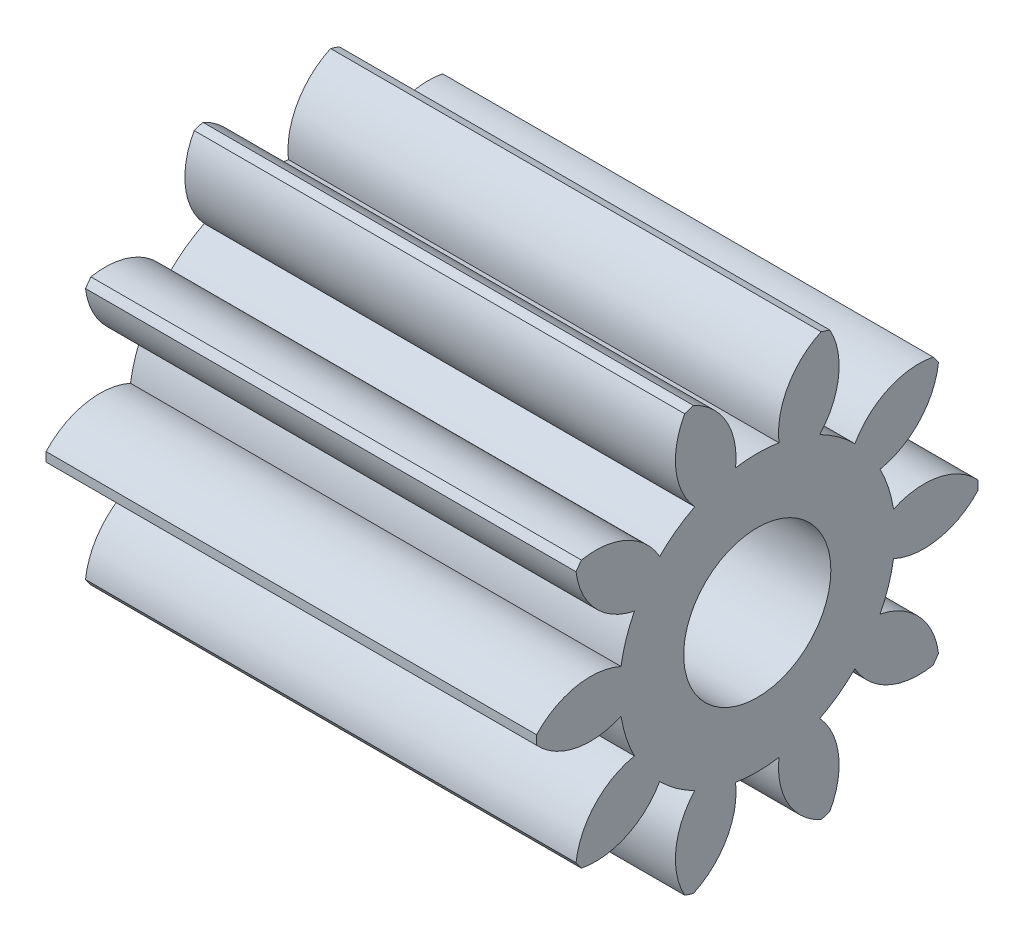
SolidWorks part; units mm, degrees
ref_plane "Plane1" through (0, 0, 0) normal (0, 0, 1) x (1, 0, 0)
ref_plane "Plane2" through (0, 0, 0) normal (0, 1, 0) x (1, 0, 0)
ref_plane "Plane3" through (0, 0, 0) normal (1, 0, 0) x (0, 0, -1)
sketch "HoldingSke" plane through (0, 0, 0) normal (0, 1, 0) x (1, 0, 0)
  line L0 (0, 0) -> (0.6565, -0.1158)
  line L1 (-15, 0) -> (100, 0) construction
  line L2 (0, 0) -> (-2.1039, 2.3779)
  line L3 (0, 0) -> (-11.863, 4.5341)
  line L4 (0, 0) -> (8.5048, 1.4996)
  line L5 (0, 0) -> (-46.8476, -17.4728)
  line L6 (0, 0) -> (-16.5793, -11.1861)
  line L7 (-2.1039, 2.3779) -> (8.6586, 51.2059)
  line L8 (-76.2, 54.61) -> (-75.3, 54.61)
  line L9 (-71.009, 38.7566) -> (-53.1078, 45.2721)
  line L10 (-76.2, 71.12) -> (104.1128, 71.12)
  line L11 (0, 0) -> (-20, 0)
  line L12 (-76.2, 101.6) -> (-76.147, 101.6)
  line L13 (24.9733, 27.94) -> (52.9518, 28.4284)
  line L14 (24.9733, 27.94) -> (24.9743, 27.94)
  line L15 (24.9733, 27.94) -> (100.4006, 29.5858)
  line L16 (-63.627, -1.5) -> (-12.827, -1.5)
  circle A0 centre (0, 0) radius 2.5
  circle A1 centre (0, 0) radius 5.624
  circle A2 centre (0, 0) radius 37.5
  circle A3 centre (0, 0) radius 2.5
  dimension "MHD" = 11.248
  dimension "Hub_dia" = 75
  dimension "Bore" = 5
  dimension "MBD" = 5
  dimension "Num_teeth" = 10
  dimension "Pitch" = 0.6667
  dimension "Overall_len" = 50
  dimension "Show_teeth" = 10
  dimension "Thickness" = 20
  dimension "OAL" = 50.0001
  dimension "T_dim" = 0.9
  dimension "Ap" = 20
  dimension "H" = 19.05
  dimension "Pitch_radius" = 180.3128
  dimension "Width" = 20
  dimension "Backlash" = 0.053
  dimension "Addendum_fac" = 1
  dimension "Dedendum_fac" = 1.25
  dimension "Clearance_fac" = 0.25
  dimension "Dedendum_add" = 0.001
  dimension "Module" = 1.5
sketch "BasProSke" plane through (0, 0, 0) normal (0, 1, 0) x (1, 0, 0)
  line L0 (-10, 0) -> (60, 0) construction
  line L1 (0, 0) -> (0, 9)
  line L2 (0, 0) -> (20, 0)
  line L3 (20, 0) -> (20, 9)
  line L4 (20, 9) -> (0, 9)
  dimension "Thickness" = 20
  dimension "Diameter" = 18
revolve "Base-Revolve" add sketch "BasProSke" angle 360 about L0
sketch "TooCutSke" plane through (0, 0, 0) normal (1, 0, 0) x (0, 0, -1)
  line L1 (0, 0) -> (0, 107) construction
  line L2 (0, 0) -> (-1.2658, 7.3924) construction
  line L3 (0, 0) -> (-4.5869, 14.117) construction
  line L4 (-1.2658, 7.3924) -> (-2.2934, 7.0585) construction
  arc A0 (0.8839, 5.5541) -> (-0.8839, 5.5541) centre (0, 0) ccw
  arc A1 (2.6378, 8.6313) -> (-2.6378, 8.6313) centre (0, 0) ccw
  circle A2 centre (0, 0) radius 7.5 construction
  circle A3 centre (0, 0) radius 7.0477 construction
  arc A4 (-0.8839, 5.5541) -> (-2.6378, 8.6313) centre (-3.8646, 5.8936) ccw
  arc A5 (2.6378, 8.6313) -> (0.8839, 5.5541) centre (3.8646, 5.8936) ccw
  dimension "Root_dia" = 11.248
  dimension "Overcut_dia" = 18.0508
  dimension "Pitch_dia" = 15
  dimension "Base_dia" = 14.0954
  dimension "Flank_rad" = 3
  dimension "Half_ang" = 18
  dimension "Half_CT" = 1.0805
extrude "ToothCut" cut sketch "TooCutSke" along normal through all
fillet "Breaks" [suppressed] radius 0.03
fillet "RootFillets" [suppressed] radius 0.376
pattern_circular "TeethCuts" count 10 every 36 about axis through (-10, 0, 0) along (1, 0, 0) of "ToothCut", "RootFillets", "Breaks"
sketch "HubNeaOneSke" plane through (0, 0, 0) normal (-1, 0, 0) x (0, 0, 1)
  circle A0 centre (0, 0) radius 5.624
  dimension "Diameter" = 11.248
extrude "HubNearOne" [suppressed] add sketch "HubNeaOneSke" along normal blind 30.0001
sketch "HubNeaBotSke" plane through (0, 0, 0) normal (-1, 0, 0) x (0, 0, 1)
  circle A0 centre (0, 0) radius 5.624
  dimension "Diameter" = 11.248
extrude "HubNearBoth" [suppressed] add sketch "HubNeaBotSke" along normal blind 15
ref_plane "FarPln" through (20, 0, 0) normal (1, 0, 0) x (0, 0, -1)
sketch "HubFarSke" plane through (20, 0, 0) normal (1, 0, 0) x (0, 0, -1)
  circle A0 centre (0, 0) radius 5.624
  dimension "Diameter" = 11.248
extrude "HubFar" [suppressed] add sketch "HubFarSke" along normal blind 15
sketch "BorSke" plane through (0, 0, 0) normal (1, 0, 0) x (0, 0, -1)
  circle A0 centre (0, 0) radius 2.5
  dimension "Diameter" = 5
extrude "Bore" cut sketch "BorSke" along normal mid plane 100.0001
sketch "KeySke" plane through (0, 0, 0) normal (1, 0, 0) x (0, 0, -1)
  line L0 (-1, 0) -> (-1, 3.4)
  line L1 (-1, 3.4) -> (1, 3.4)
  line L2 (1, 3.4) -> (1, 0)
  line L3 (0, 0) -> (0, 34) construction
  line L4 (-1, 0) -> (1, 0)
  dimension "Offset" = 3.4
extrude "Keyway" [suppressed] cut sketch "KeySke" along normal mid plane 100.0001
pattern_circular "Keyway2" [suppressed] count 2 every 90 about axis through (-10, 0, 0) along (1, 0, 0)
sketch "Çizim1" plane through (20, 0, 0) normal (1, 0, 0) x (0, 0, -1)
  circle A0 centre (0, 0) radius 3
  dimension "D1" = 6
extrude "Kes-Ekstrüzyon1" cut sketch "Çizim1" against normal blind 23
equation "' \"Module@HoldingSke\" = 6.35"
equation "' \"Num_teeth@HoldingSke\" = 12"
equation "' \"Ap@HoldingSke\" =  20"
equation "' \"Ap@HoldingSke\" = 20"
equation "' \"Width@HoldingSke\" = 0.5 * 25.4"
equation "' \"Hub_dia@HoldingSke\"= 1 * 25.4"
equation "' \"Hub_dia@HoldingSke\" = 1 * 25.4"
equation "' \"Overall_len@HoldingSke\" = 1.0 * 25.4"
equation "' \"Bore@HoldingSke\" = 0.75 * 25.4"
equation "' \"T_dim@HoldingSke\" = 0.1 * 25.4"
equation "' \"Width@KeySke\" = 0.25 * 25.4"
equation "' \"Show_teeth@HoldingSke\" = 13"
equation "' \"Backlash@HoldingSke\" = 0.009 * 25.4"
equation "' \"Addendum_fac@HoldingSke\" = 1.0"
equation "' \"Dedendum_fac@HoldingSke\" = 1.25"
equation "' \"Dedendum_add@HoldingSke\" = 0.00005 * 25.4"
equation "' \"Clearance_fac@HoldingSke\" = 0.25"
equation "\"Pitch@HoldingSke\" = 1 / \"Module@HoldingSke\""
equation "\"Overcut_dia@TooCutSke\" = (\"Num_teeth@HoldingSke\" + 2 * \"Addendum_fac@HoldingSke\") / \"Pitch@HoldingSke\" + 0.002 * 25.4"
equation "\"Pitch_dia@TooCutSke\" = \"Num_teeth@HoldingSke\" / \"Pitch@HoldingSke\""
equation "\"Base_dia@TooCutSke\" = \"Num_teeth@HoldingSke\" / \"Pitch@HoldingSke\" * cos((\"Ap@HoldingSke\"  * 3.14159265 / 180))"
equation "\"Root_dia@TooCutSke\" = (\"Num_teeth@HoldingSke\" + 2) / \"Pitch@HoldingSke\" - 2 * (\"Addendum_fac@HoldingSke\" + \"Dedendum_fac@HoldingSke\") / \"Pitch@HoldingSke\" - \"Dedendum_add@HoldingSke\" * 2"
equation "\"Half_ang@TooCutSke\" = 180 / \"Num_teeth@HoldingSke\""
equation "\"Half_CT@TooCutSke\" = \"Num_teeth@HoldingSke\" / \"Pitch@HoldingSke\" * sin((3.14159265 / 2 / \"Num_teeth@HoldingSke\")) / 2 - 7 * \"Backlash@HoldingSke\" / 4"
equation "\"Flank_rad@TooCutSke\" = \"Num_teeth@HoldingSke\" / \"Pitch@HoldingSke\" / 5"
equation "\"Radius@RootFillets\" = \"Clearance_fac@HoldingSke\" / \"Pitch@HoldingSke\" + \"Dedendum_add@HoldingSke\""
equation "\"Break_rad@Breaks\" = 0.02 / \"Pitch@HoldingSke\""
equation "\"Thickness@HoldingSke\" = \"Width@HoldingSke\""
equation "\"OAL@HoldingSke\" = \"Thickness@HoldingSke\""
equation "\"MHD@HoldingSke\" = (\"Num_teeth@HoldingSke\" + 2) / \"Pitch@HoldingSke\" - 2 * (\"Addendum_fac@HoldingSke\" + \"Dedendum_fac@HoldingSke\")  / \"Pitch@HoldingSke\" - \"Dedendum_add@HoldingSke\" * 2"
equation "\"MBD@HoldingSke\" = (\"Num_teeth@HoldingSke\" + 2) / \"Pitch@HoldingSke\" - 2 * (\"Addendum_fac@HoldingSke\" + \"Dedendum_fac@HoldingSke\")  / \"Pitch@HoldingSke\" - \"Dedendum_add@HoldingSke\" * 2 - 0.002 * 25.4"
equation "\"MHD@HoldingSke\" = ((sgn( \"MHD@HoldingSke\" - \"Hub_dia@HoldingSke\" )-1)*( \"MHD@HoldingSke\" - \"Hub_dia@HoldingSke\" ))/-2+ \"Hub_dia@HoldingSke\""
equation "\"MBD@HoldingSke\" = ((sgn( \"MBD@HoldingSke\" - \"Bore@HoldingSke\" )-1)*( \"MBD@HoldingSke\" - \"Bore@HoldingSke\" ))/-2+ \"Bore@HoldingSke\""
equation "\"OAL@HoldingSke\" = ((sgn( \"OAL@HoldingSke\" - \"Overall_len@HoldingSke\" )+1)*( \"OAL@HoldingSke\" - \"Overall_len@HoldingSke\" ))/2 + \"Overall_len@HoldingSke\" + 0.000002 * 25.4"
equation "\"Num_teeth@TeethCuts\" = int( \"Show_teeth@HoldingSke\" ) + 1"
equation "\"Num_teeth@TeethCuts\" = ((sgn( \"Num_teeth@TeethCuts\" - \"Num_teeth@HoldingSke\" )-1)*( \"Num_teeth@TeethCuts\" - \"Num_teeth@HoldingSke\" ))/-2+ \"Num_teeth@HoldingSke\""
equation "\"Num_teeth@TeethCuts\" = ((sgn( \"Num_teeth@TeethCuts\" - 2.0)+1)*( \"Num_teeth@TeethCuts\" - 2.0))/2 +2.0"
equation "\"Angle@TeethCuts\" = 360.0 / \"Num_teeth@HoldingSke\""
equation "\"Diameter@BasProSke\" = (\"Num_teeth@HoldingSke\" + 2 * \"Addendum_fac@HoldingSke\") / \"Pitch@HoldingSke\""
equation "\"Thickness@BasProSke\"  = \"Thickness@HoldingSke\""
equation "' \"Fillet_rad@BasProSke\" =  \"Thickness@HoldingSke\" * 0.05"
equation "' \"Fillet_rad@BasProSke\" = \"Thickness@HoldingSke\" * 0.05"
equation "\"MHD@HoldingSke\" = ((sgn( \"MHD@HoldingSke\" - \"Root_dia@TooCutSke\" )-1)*( \"MHD@HoldingSke\" - \"Root_dia@TooCutSke\" ))/-2+ \"Root_dia@TooCutSke\""
equation "\"Diameter@HubNeaOneSke\" = \"MHD@HoldingSke\""
equation "\"Length@HubNearOne\" = \"OAL@HoldingSke\" - \"Thickness@BasProSke\""
equation "\"Diameter@HubNeaBotSke\" = \"MHD@HoldingSke\""
equation "\"Length@HubNearBoth\" = ( \"OAL@HoldingSke\" - \"Thickness@BasProSke\" ) / 2.0"
equation "\"Thickness@FarPln\" = \"Thickness@BasProSke\""
equation "\"Diameter@HubFarSke\" = \"MHD@HoldingSke\""
equation "\"Length@HubFar\" = ( \"OAL@HoldingSke\" - \"Thickness@BasProSke\" ) / 2.0"
equation "\"Diameter@BorSke\" = \"MBD@HoldingSke\""
equation "\"D1@Bore\" = \"OAL@HoldingSke\" * 2.0"
equation "\"D1@Keyway\" = \"OAL@HoldingSke\" * 2.0"
equation "\"Offset@KeySke\" = \"T_dim@HoldingSke\" + \"MBD@HoldingSke\" / 2.0"
